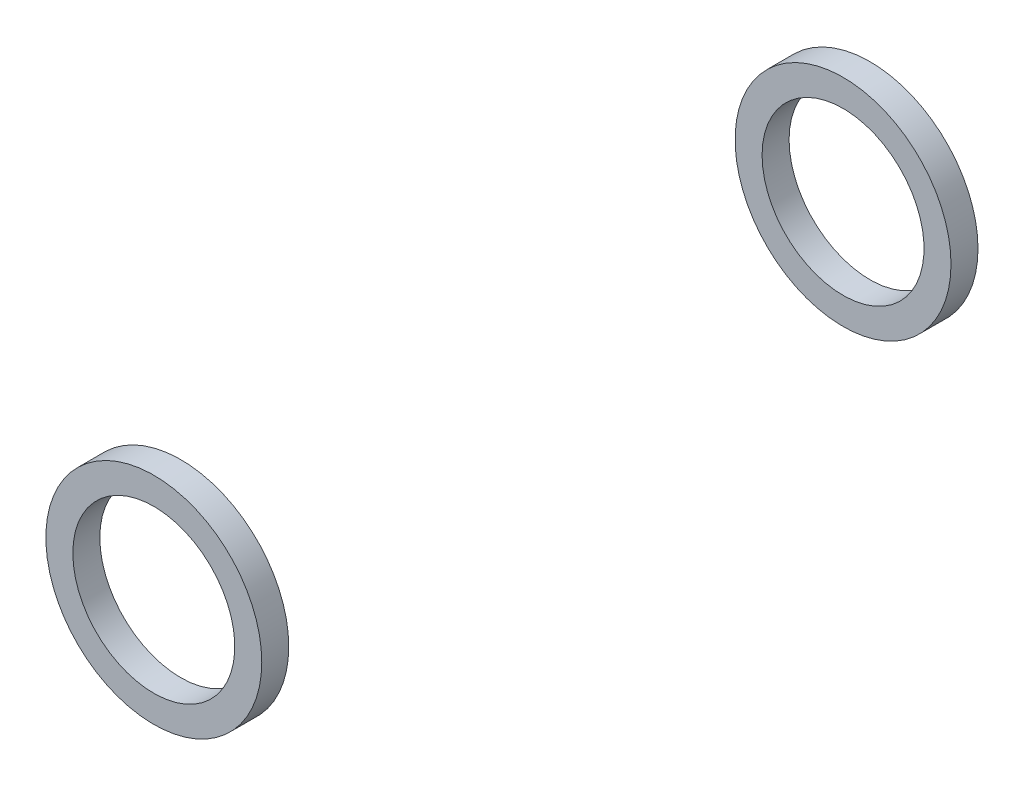
SolidWorks part; units mm, degrees
ref_plane "Front" through (0, 0, 0) normal (0, 0, 1) x (1, 0, 0)
ref_plane "Top" through (0, 0, 0) normal (0, 1, 0) x (1, 0, 0)
ref_plane "Right" through (0, 0, 0) normal (1, 0, 0) x (0, 0, -1)
sketch "Sketch1" plane through (0, 0, 0) normal (0, 0, 1) x (1, 0, 0)
  circle A0 centre (0, 0) radius 12.7
  dimension "D1" = 25.4
extrude "Boss-Extrude1" add sketch "Sketch1" along normal blind 61.345
sketch "Sketch2" plane through (0, 0, 61.345) normal (0, 0, 1) x (1, 0, 0)
  circle A0 centre (0, 0) radius 18
  circle A1 centre (0, 0) radius 20
  dimension "D1" = 36
  dimension "D2" = 40
extrude "Cut-Extrude2" cut sketch "Sketch2" against normal blind 1.85
sketch "Sketch6" plane through (0, 0, 61.345) normal (0, 0, 1) x (1, 0, 0)
  circle A0 centre (0, 0) radius 20
  dimension "D1" = 40
extrude "Boss-Extrude2" add sketch "Sketch6" along normal blind 5
mirror "Mirror2" about plane through (0, 0, 0) normal (0, 0, 1) of bodies 106
sketch "Sketch7" plane through (0, 0, -66.345) normal (0, 0, -1) x (-1, 0, 0)
  circle A0 centre (0, 0) radius 15
  dimension "D1" = 30
extrude "Cut-Extrude3" cut sketch "Sketch7" against normal through all both and the other way through all
